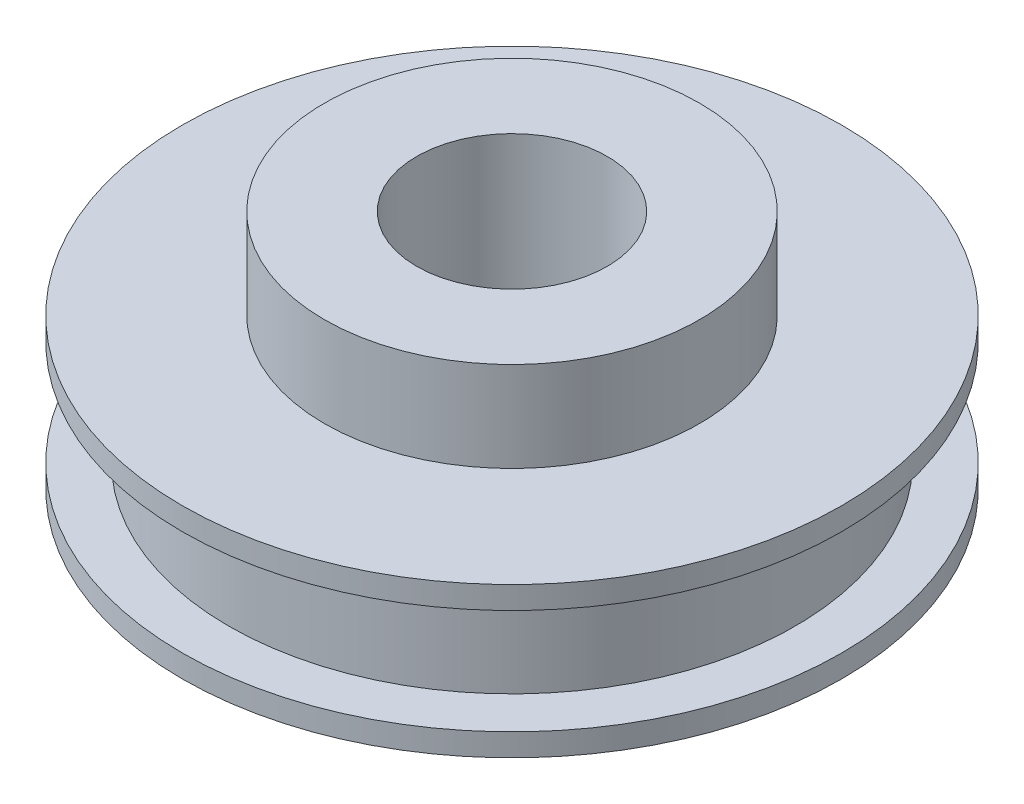
SolidWorks part; units mm, degrees
ref_plane "Front Plane" through (0, 0, 0) normal (0, 0, 1) x (1, 0, 0)
ref_plane "Top Plane" through (0, 0, 0) normal (0, 1, 0) x (1, 0, 0)
ref_plane "Right Plane" through (0, 0, 0) normal (1, 0, 0) x (0, 0, -1)
sketch "Sketch1" plane through (0, 0, 0) normal (0, 0, 1) x (1, 0, 0)
  line L0 (0, 0) -> (0, 16)
  line L1 (0, 16) -> (-12.5, 16)
  line L2 (-12.5, 16) -> (-12.5, 10)
  line L3 (-12.5, 10) -> (-21.971, 10)
  line L4 (-21.971, 10) -> (-21.971, 8.5)
  line L5 (-21.971, 8.5) -> (-18.875, 8.5)
  line L6 (-18.875, 8.5) -> (-18.875, 1.5)
  line L7 (-18.875, 1.5) -> (-21.971, 1.5)
  line L8 (-21.971, 1.5) -> (-21.971, 0)
  line L9 (-21.971, 0) -> (0, 0)
  dimension "D1" = 6
  dimension "D2" = 16
  dimension "D3" = 12.5
  dimension "D4" = 21.971
  dimension "D5" = 18.875
  dimension "D6" = 7
revolve "Revolve1" add sketch "Sketch1" angle 360 about L0
sketch "Sketch2" plane through (0, 16, 0) normal (0, 1, 0) x (1, 0, 0)
  circle A0 centre (0, 0) radius 6.35
  dimension "D1" = 12.7
extrude "Cut-Extrude1" cut sketch "Sketch2" against normal through all
